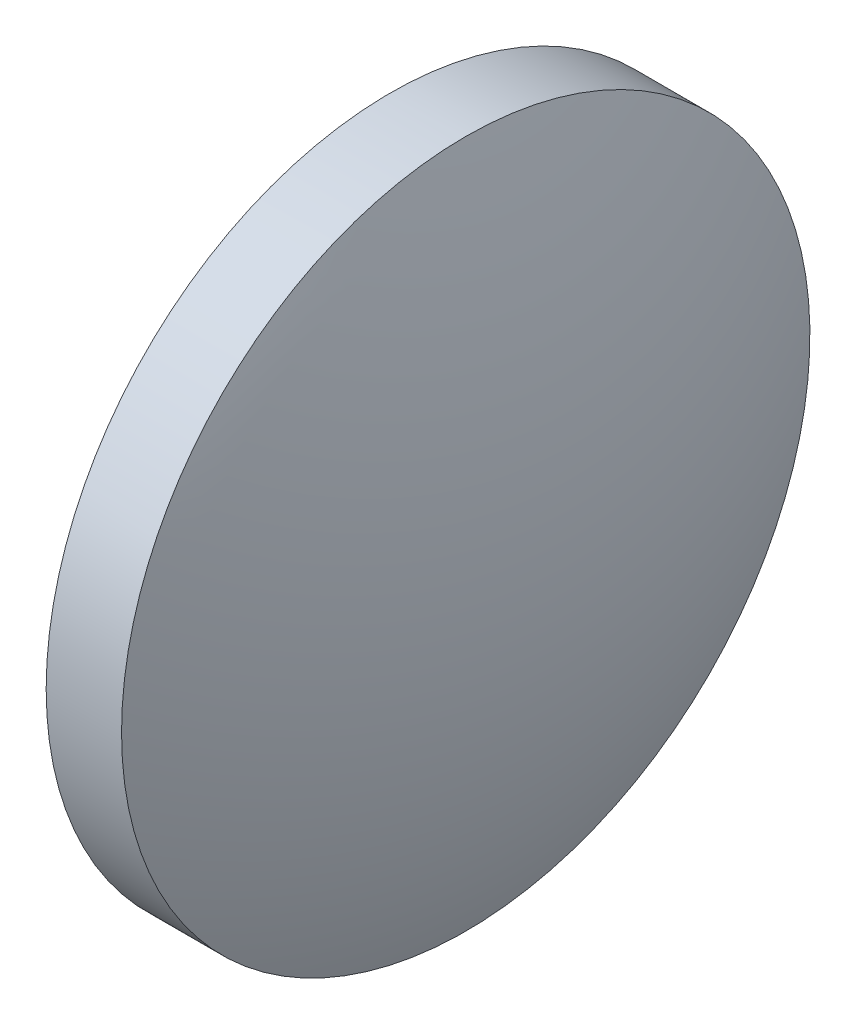
SolidWorks part; units mm, degrees
ref_plane "前视基准面" through (0, 0, 0) normal (0, 0, 1) x (1, 0, 0)
ref_plane "上视基准面" through (0, 0, 0) normal (0, 1, 0) x (1, 0, 0)
ref_plane "右视基准面" through (0, 0, 0) normal (1, 0, 0) x (0, 0, -1)
sketch "草图2" plane through (0, 0, 0) normal (0, 0, 1) x (1, 0, 0)
  line L0 (548.8631, 125.1721) -> (559.1972, 125.1721) construction
  line L1 (551.2666, 125.1721) -> (551.2666, 135.1721)
  line L2 (555.4666, 125.1721) -> (551.2666, 125.1721)
  line L5 (551.2666, 135.1721) -> (553.4566, 135.1721)
  arc A0 (555.4666, 125.1721) -> (553.4566, 135.1721) centre (529.586, 125.1721) ccw
revolve "旋转2" add sketch "草图2" angle 360 about L0
